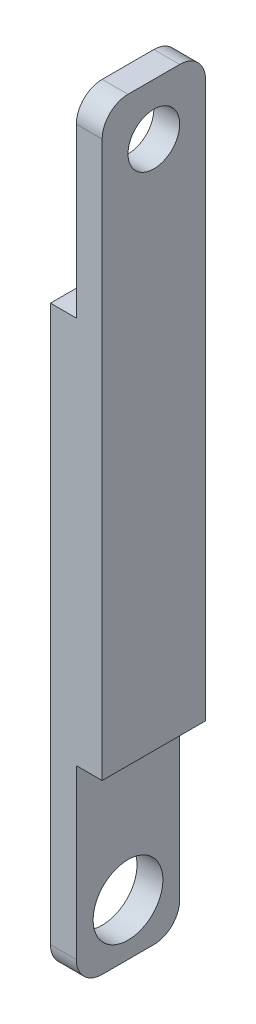
SolidWorks part; units mm, degrees
ref_plane "Ön Düzlem" through (0, 0, 0) normal (0, 0, 1) x (1, 0, 0)
ref_plane "Üst Düzlem" through (0, 0, 0) normal (0, 1, 0) x (1, 0, 0)
ref_plane "Sağ Düzlem" through (0, 0, 0) normal (1, 0, 0) x (0, 0, -1)
sketch "Sketch1" plane through (0, 0, 0) normal (1, 0, 0) x (0, 0, -1)
  line L1 (-20, 150) -> (20, 150)
  line L2 (-20, 150) -> (-20, -150)
  line L3 (-20, -150) -> (20, -150)
  line L4 (20, 150) -> (20, -150)
  line L5 (-20, 150) -> (20, -150) construction
  line L6 (-20, -150) -> (20, 150) construction
  point P0 (0, 0)
  dimension "D1" = 40
  dimension "D2" = 300
extrude "Boss-Extrude1" add sketch "Sketch1" along normal blind 20
sketch "Sketch2" plane through (0, 0, 0) normal (-1, 0, 0) x (0, 0, 1)
  line L0 (20, 150) -> (20, -150) construction
  line L1 (-20, 150) -> (20, 150)
  line L2 (-20, 150) -> (-20, 75)
  line L3 (-20, 75) -> (20, 75)
  line L4 (20, 150) -> (20, 75)
  dimension "D1" = 75
extrude "Cut-Extrude1" cut sketch "Sketch2" against normal blind 10
sketch "Sketch3" plane through (20, 0, 0) normal (1, 0, 0) x (0, 0, -1)
  line L0 (20, -150) -> (20, 150) construction
  line L1 (-20, -150) -> (20, -150)
  line L2 (-20, -150) -> (-20, -75)
  line L3 (-20, -75) -> (20, -75)
  line L4 (20, -150) -> (20, -75)
  dimension "D1" = 75
extrude "Cut-Extrude2" cut sketch "Sketch3" against normal blind 10
sketch "Sketch4" plane through (0, 0, 0) normal (-1, 0, 0) x (0, 0, 1)
  line L0 (20, -150) -> (-20, -150) construction
  circle A0 centre (0, -130) radius 13.5
  dimension "D1" = 20
extrude "Cut-Extrude3" cut sketch "Sketch4" against normal blind 10
fillet "Fillet1" radius 10 4 edges at (5, -150, -20) (5, -150, 20) (15, 150, -20) (15, 150, 20)
sketch "Sketch5" plane through (20, 0, 0) normal (1, 0, 0) x (0, 0, -1)
  line L0 (10, 150) -> (-10, 150) construction
  circle A0 centre (0, 130) radius 10
  dimension "D1" = 20
extrude "Cut-Extrude4" cut sketch "Sketch5" against normal blind 10
